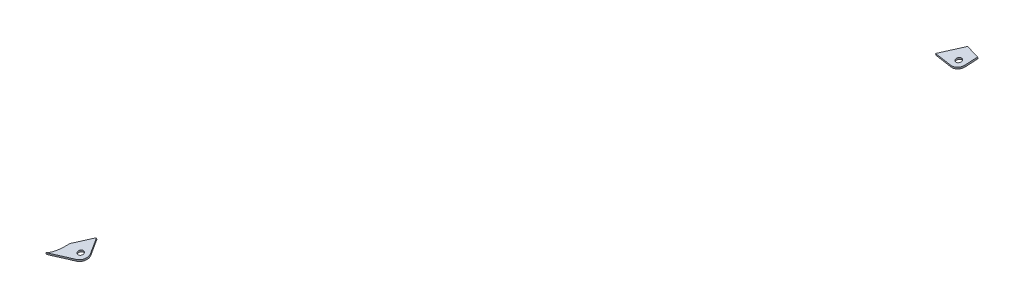
SolidWorks part; units mm, degrees
material "Stal węglowa"
ref_plane "Płaszczyzna XY" through (0, 0, 0) normal (0, 0, 1) x (1, 0, 0)
ref_plane "Płaszczyzna XZ" through (0, 0, 0) normal (0, 1, 0) x (1, 0, 0)
ref_plane "Płaszczyzna YZ" through (0, 0, 0) normal (1, 0, 0) x (0, 0, -1)
sketch "Szkic1" plane through (0, 365.9457, 71.1326) normal (0, -0.9816, -0.1908) x (-1, 0, 0)
  line L0 (-1362.9238, -419.8541) -> (-1364.538, -407.3199)
  line L1 (-1353.9675, -426.7668) -> (-1334.8084, -424.2994)
  line L4 (-952.8484, -984.8258) -> (-944.0551, -969.1403)
  line L5 (-948.5109, -996.2894) -> (-923.5699, -1005.0113)
  circle A2 centre (-945.8701, -988.7378) radius 3
  circle A3 centre (-1354.9893, -418.8323) radius 3
  arc A4 (-1362.9238, -419.8541) -> (-1353.9675, -426.7668) centre (-1354.9893, -418.8323) ccw
  arc A5 (-952.8484, -984.8258) -> (-948.5109, -996.2894) centre (-945.8701, -988.7378) ccw
  spline S2 degree 3 poles (-931.5751, -986.5395) (-935.7366, -980.7378) (-939.8966, -974.9381) (-944.0551, -969.1403) knots 0 0 0 0 0.029476 0.029476 0.029476 0.029476 weights 1 0.999984 0.999968 0.999953
  spline S5 degree 3 poles (-923.5699, -1005.0113) (-923.9781, -1004.7441) (-924.3614, -1004.442) (-924.9333, -1003.9224) (-925.1352, -1003.7234) (-925.5212, -1003.3152) (-925.7062, -1003.1051) (-926.5965, -1002.0293) (-927.2013, -1001.087) (-928.266, -999.1061) (-928.715, -998.0863) (-929.5017, -996.0077) (-929.8387, -994.9486) (-930.4291, -992.8009) (-930.6829, -991.7089) (-931.1739, -989.2588) (-931.3939, -987.9) (-931.5751, -986.5395) knots 0.533257 0.533257 0.533257 0.533257 0.546875 0.546875 0.554688 0.554688 0.5625 0.5625 0.59375 0.59375 0.625 0.625 0.65625 0.65625 0.6875 0.6875 0.726253 0.726253 0.726253 0.726253
  spline S7 degree 3 poles (-1349.7018, -403.5304) (-1355.0231, -404.9951) (-1359.9762, -406.2564) (-1364.538, -407.3199) knots 0.941559 0.941559 0.941559 0.941559 0.993311 0.993311 0.993311 0.993311 weights 0.880926 0.911423 0.946038 0.984774
  spline S8 degree 3 poles (-1334.8084, -424.2994) (-1339.7757, -417.3724) (-1344.7402, -410.4494) (-1349.7018, -403.5304) knots 0.963874 0.963874 0.963874 0.963874 1 1 1 1 weights 0.999942 0.999961 0.99998 1
  dimension "D1" = 5
extrude "Dodanie-wyciągnięcie1" add sketch "Szkic1" against normal blind 2
